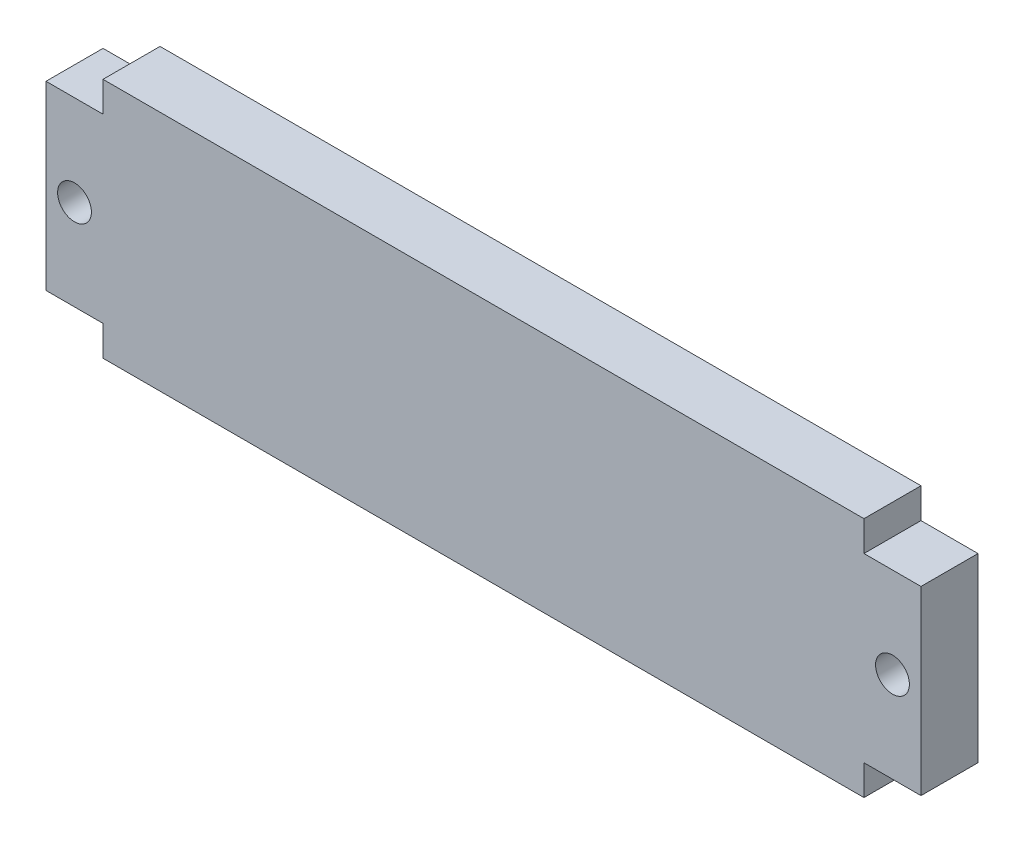
SolidWorks part; units mm, degrees
ref_plane "Front Plane" through (0, 0, 0) normal (0, 0, 1) x (1, 0, 0)
ref_plane "Top Plane" through (0, 0, 0) normal (0, 1, 0) x (1, 0, 0)
ref_plane "Right Plane" through (0, 0, 0) normal (1, 0, 0) x (0, 0, -1)
sketch "Sketch1" plane through (0, 0, 0) normal (0, 0, 1) x (1, 0, 0)
  line L1 (0, 0) -> (91.9988, 0)
  line L2 (0, 0) -> (0, 25.4)
  line L3 (0, 25.4) -> (91.9988, 25.4)
  line L4 (91.9988, 0) -> (91.9988, 25.4)
  dimension "D1" = 25.4
  dimension "D2" = 91.9988
extrude "Boss-Extrude1" add sketch "Sketch1" against normal blind 5.9944
sketch "Sketch2" plane through (0, 0, 0) normal (0, 0, 1) x (1, 0, 0)
  line L0 (0, 12.7) -> (91.9988, 12.7) construction
  line L1 (0, 25.4) -> (0, 0) construction
  line L2 (91.9988, 0) -> (91.9988, 25.4) construction
  line L3 (45.9994, 25.4) -> (45.9994, 0) construction
  line L4 (91.9988, 25.4) -> (0, 25.4) construction
  line L5 (0, 0) -> (91.9988, 0) construction
  circle A0 centre (2.9972, 12.7) radius 1.778
  circle A1 centre (89.0016, 12.7) radius 1.778
  dimension "D1" = 3.556
  dimension "D2" = 2.9972
extrude "Cut-Extrude1" cut sketch "Sketch2" against normal through all
sketch "Sketch3" plane through (0, 0, 0) normal (0, 0, 1) x (1, 0, 0)
  line L0 (45.9994, 25.4) -> (45.9994, 0) construction
  line L1 (0, 25.4) -> (5.9944, 25.4)
  line L2 (0, 25.4) -> (0, 22.225)
  line L3 (0, 22.225) -> (5.9944, 22.225)
  line L4 (5.9944, 25.4) -> (5.9944, 22.225)
  line L5 (91.9988, 25.4) -> (0, 25.4) construction
  line L6 (0, 0) -> (91.9988, 0) construction
  line L7 (0, 12.7) -> (91.9988, 12.7) construction
  line L8 (0, 25.4) -> (0, 0) construction
  line L9 (91.9988, 0) -> (91.9988, 25.4) construction
  line L10 (91.9988, 22.225) -> (86.0044, 22.225)
  line L11 (86.0044, 25.4) -> (86.0044, 22.225)
  line L12 (91.9988, 25.4) -> (86.0044, 25.4)
  line L13 (91.9988, 25.4) -> (91.9988, 22.225)
  line L14 (91.9988, 0) -> (91.9988, 3.175)
  line L15 (91.9988, 0) -> (86.0044, 0)
  line L16 (86.0044, 0) -> (86.0044, 3.175)
  line L17 (91.9988, 3.175) -> (86.0044, 3.175)
  line L18 (0, 3.175) -> (5.9944, 3.175)
  line L19 (5.9944, 0) -> (5.9944, 3.175)
  line L20 (0, 0) -> (5.9944, 0)
  line L21 (0, 0) -> (0, 3.175)
  dimension "D1" = 5.9944
  dimension "D2" = 3.175
extrude "Cut-Extrude2" cut sketch "Sketch3" against normal through all
